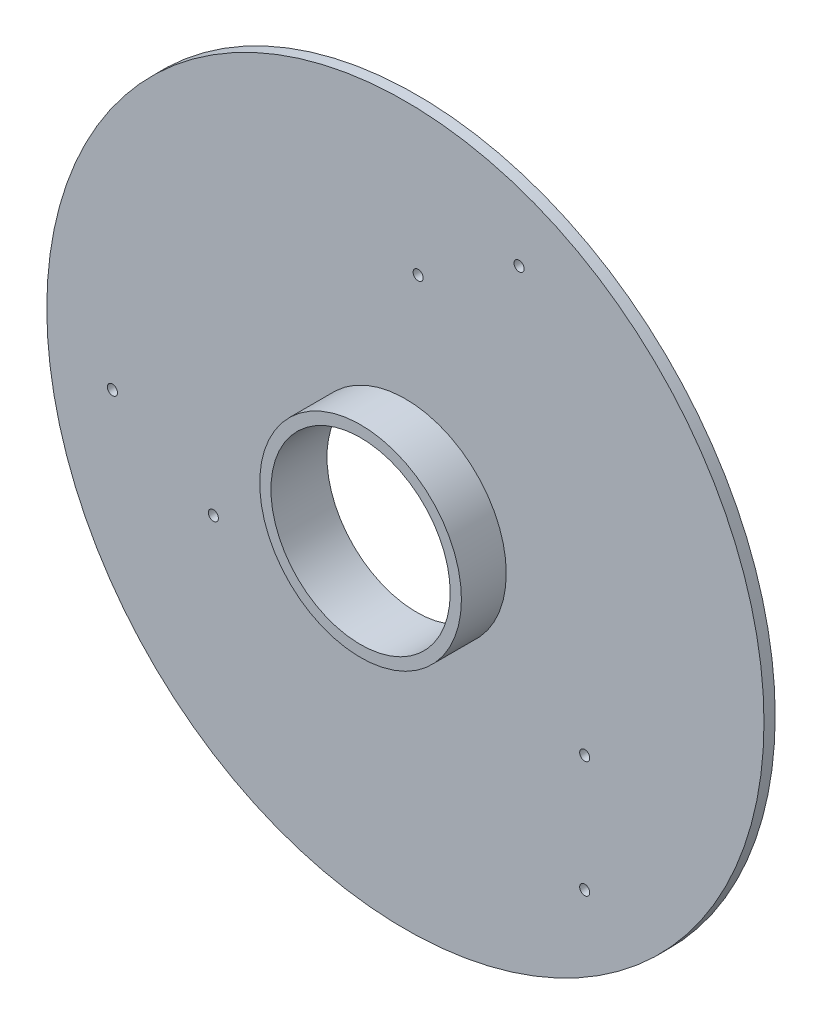
SolidWorks part; units mm, degrees
ref_plane "Front Plane" through (0, 0, 0) normal (0, 0, 1) x (1, 0, 0)
ref_plane "Top Plane" through (0, 0, 0) normal (0, 1, 0) x (1, 0, 0)
ref_plane "Right Plane" through (0, 0, 0) normal (1, 0, 0) x (0, 0, -1)
sketch "Sketch2" plane through (0, 0, 0) normal (0, 0, 1) x (1, 0, 0)
  line L0 (0, 0) -> (800, 0) construction
  line L1 (800, 0) -> (800, -527.5) construction
  line L2 (800, -527.5) -> (800, -1047.5) construction
  line L3 (800, 0) -> (1744.3, 0) construction
  line L4 (1744.3, 0) -> (1744.3, -272.5) construction
  circle A0 centre (0, 0) radius 1600
  circle A1 centre (800, -527.5) radius 22.5
  circle A2 centre (800, -1047.5) radius 22.5
  circle A3 centre (-856.8284, -429.0703) radius 22.5
  circle A4 centre (-1307.1616, -169.0703) radius 22.5
  circle A5 centre (56.8284, 956.5703) radius 22.5
  circle A6 centre (507.1616, 1216.5703) radius 22.5
  point P20 (0, 0)
  dimension "D1" = 3200
  dimension "D5" = 45
  dimension "D2" = 800
  dimension "D3" = 527.5
  dimension "D4" = 520
  dimension "D6" = 944.3
  dimension "D7" = 272.5
  dimension "D8" = 3
extrude "Boss-Extrude1" add sketch "Sketch2" along normal blind 50
sketch "Sketch3" plane through (0, 0, 50) normal (0, 0, 1) x (1, 0, 0)
  circle A0 centre (0, 0) radius 400
  dimension "D1" = 800
extrude "Cut-Extrude1" cut sketch "Sketch3" against normal through all
sketch "Sketch4" plane through (0, 0, 50) normal (0, 0, 1) x (1, 0, 0)
  circle A0 centre (0, 0) radius 450
  dimension "D1" = 900
extrude "Boss-Extrude2" add sketch "Sketch4" along normal blind 200
sketch "Sketch5" plane through (0, 0, 250) normal (0, 0, 1) x (1, 0, 0)
  circle A0 centre (0, 0) radius 400
  dimension "D1" = 800
extrude "Cut-Extrude2" cut sketch "Sketch5" against normal through all
